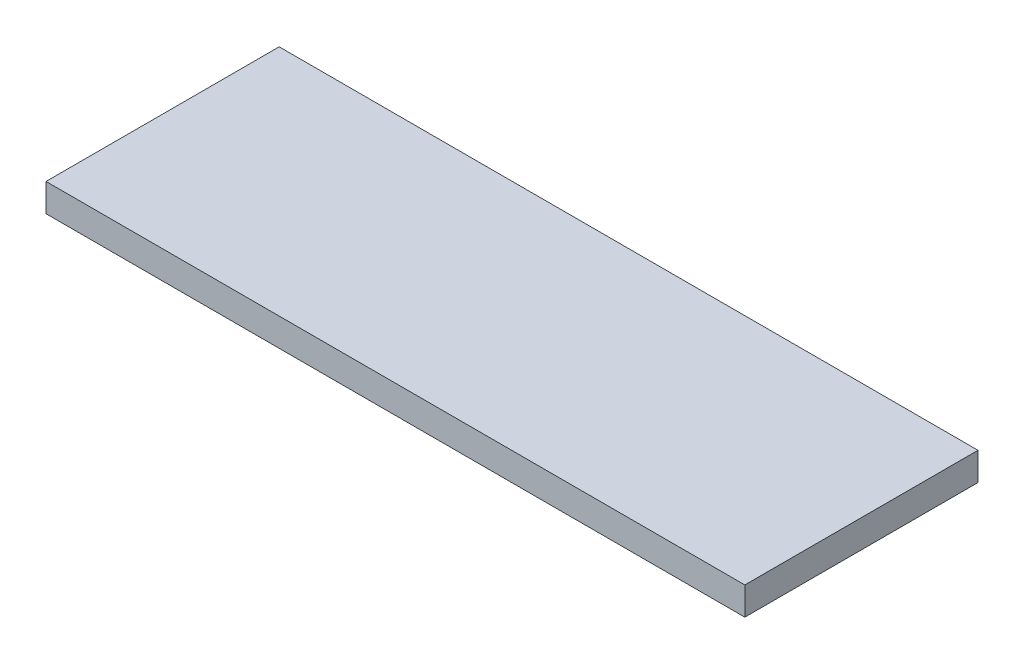
SolidWorks part; units mm, degrees
ref_plane "Front Plane" through (0, 0, 0) normal (0, 0, 1) x (1, 0, 0)
ref_plane "Top Plane" through (0, 0, 0) normal (0, 1, 0) x (1, 0, 0)
ref_plane "Right Plane" through (0, 0, 0) normal (1, 0, 0) x (0, 0, -1)
sketch "Sketch1" plane through (0, 0, 0) normal (0, 1, 0) x (1, 0, 0)
  line L1 (0, 0) -> (-150, 0)
  line L2 (0, 0) -> (0, 50.05)
  line L3 (0, 50.05) -> (-150, 50.05)
  line L4 (-150, 0) -> (-150, 50.05)
  dimension "D1" = 50.05
  dimension "D2" = 150
extrude "Boss-Extrude2" add sketch "Sketch1" along normal blind 6
